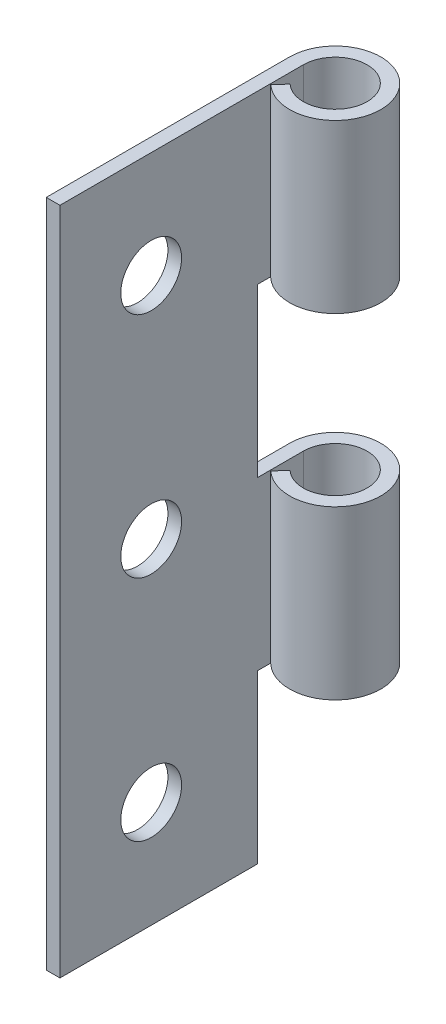
SolidWorks part; units mm, degrees
ref_plane "Front Plane" through (0, 0, 0) normal (0, 0, 1) x (1, 0, 0)
ref_plane "Top Plane" through (0, 0, 0) normal (0, 1, 0) x (1, 0, 0)
ref_plane "Right Plane" through (0, 0, 0) normal (1, 0, 0) x (0, 0, -1)
sketch "Sketch1" plane through (0, 0, 0) normal (1, 0, 0) x (0, 0, -1)
  line L1 (0, 0) -> (13, 0)
  line L2 (0, 0) -> (0, 44)
  line L3 (0, 44) -> (13, 44)
  line L4 (13, 0) -> (13, 44)
  dimension "D1" = 44
  dimension "D2" = 13
extrude "Boss-Extrude1" add sketch "Sketch1" along normal blind 0.9
sketch "Sketch2" plane through (0, 0, 0) normal (0, -1, 0) x (1, 0, 0)
  line L0 (0, -13) -> (50000, -13) construction
  line L1 (6, -10.5613) -> (6, -50010.5613) construction
  line L2 (0, -13) -> (0, 49987) construction
  line L3 (6, -19) -> (-49994, -19) construction
  line L4 (0, -13) -> (35355.3391, -35368.3391) construction
  line L5 (0, -19) -> (35355.3391, 35336.3391) construction
  line L6 (0, -16) -> (0, -13)
  line L7 (0.9, -13) -> (0.9, -16)
  line L8 (1.5685, -14.4635) -> (0.955, -13.805)
  line L9 (0.9, -13) -> (0, -13)
  arc A1 (0.9, -16) -> (1.5685, -14.4635) centre (3, -16) ccw
  arc A2 (0, -16) -> (0.955, -13.805) centre (3, -16) ccw
  dimension "D1" = 6
  dimension "D2" = 6
extrude "Boss-Extrude2" add sketch "Sketch2" against normal up to vertex (44 mm away)
sketch "Sketch3" plane through (0, 0, 0) normal (-1, 0, 0) x (0, 0, 1)
  line L0 (0, 22) -> (-50000, 22) construction
  line L1 (0, 44) -> (0, 0) construction
  line L2 (0, 7) -> (-50000, 7) construction
  line L3 (0, 37) -> (-50000, 37) construction
  line L4 (-16, 0) -> (-16, 50000) construction
  line L5 (-19, 0) -> (-13, 0) construction
  line L6 (-6, 0) -> (-6, 50000) construction
  line L7 (-13, 0) -> (-13, 44) construction
  line L42 (-19, 0) -> (-13, 0)
  line L47 (-19, 0) -> (-19, 11)
  line L48 (-19, 11) -> (-13, 11)
  line L49 (-13, 0) -> (-13, 11)
  line L50 (-19, 44) -> (-19, 0) construction
  line L51 (-19, 22) -> (-13, 22)
  line L52 (-19, 22) -> (-19, 33)
  line L53 (-19, 33) -> (-13, 33)
  line L54 (-13, 22) -> (-13, 33)
  line L55 (-13, 44) -> (-19, 44) construction
  circle A0 centre (-6, 7) radius 2
  circle A1 centre (-6, 22) radius 2
  circle A2 centre (-6, 37) radius 2
  point P4 (0, 22)
  point P13 (-16, 0)
  dimension "D4" = 4
  dimension "D5" = 4
  dimension "D6" = 4
  dimension "D1" = 15
  dimension "D2" = 15
  dimension "D3" = 10
  dimension "D7" = 11
  dimension "D8" = 11
  dimension "D9" = 11
  dimension "D10" = 11
extrude "Cut-Extrude1" cut sketch "Sketch3" against normal blind 127
